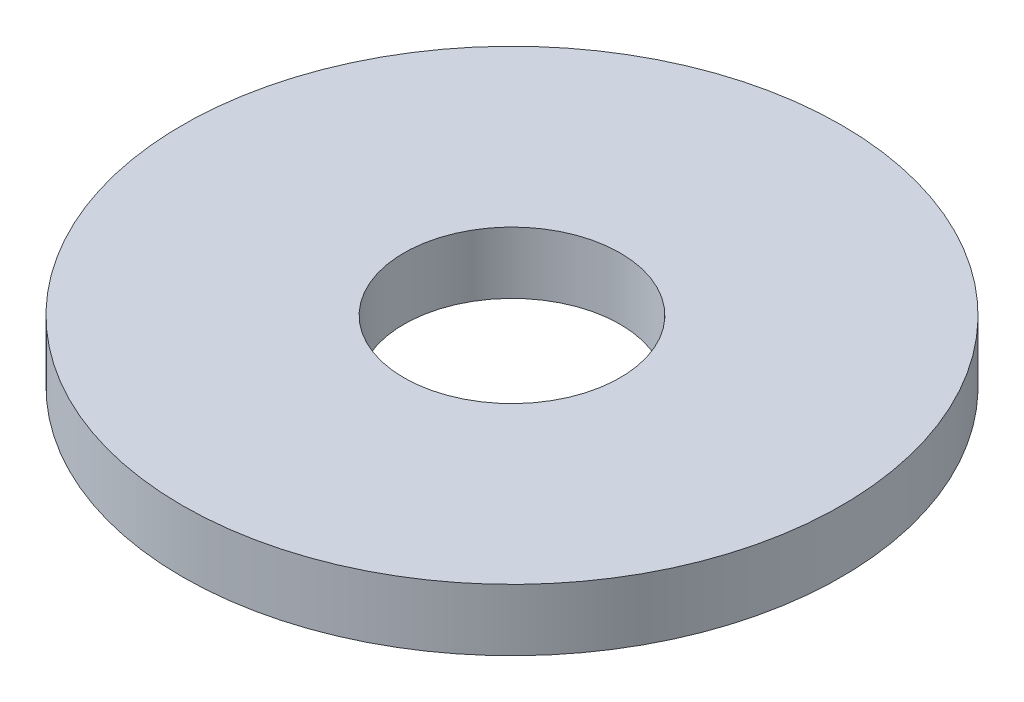
SolidWorks part; units mm, degrees
material "1023 Carbon Steel Sheet (SS)"
ref_plane "Front Plane" through (0, 0, 0) normal (0, 0, 1) x (1, 0, 0)
ref_plane "Top Plane" through (0, 0, 0) normal (0, 1, 0) x (1, 0, 0)
ref_plane "Right Plane" through (0, 0, 0) normal (1, 0, 0) x (0, 0, -1)
sketch "Sketch1" plane through (0, 0, 0) normal (0, 1, 0) x (1, 0, 0)
  circle A0 centre (0, 0) radius 16.6687
  circle A1 centre (0, 0) radius 50.8
  dimension "D1" = 33.3375
  dimension "D2" = 101.6
extrude "Boss-Extrude1" add sketch "Sketch1" along normal blind 9.525
